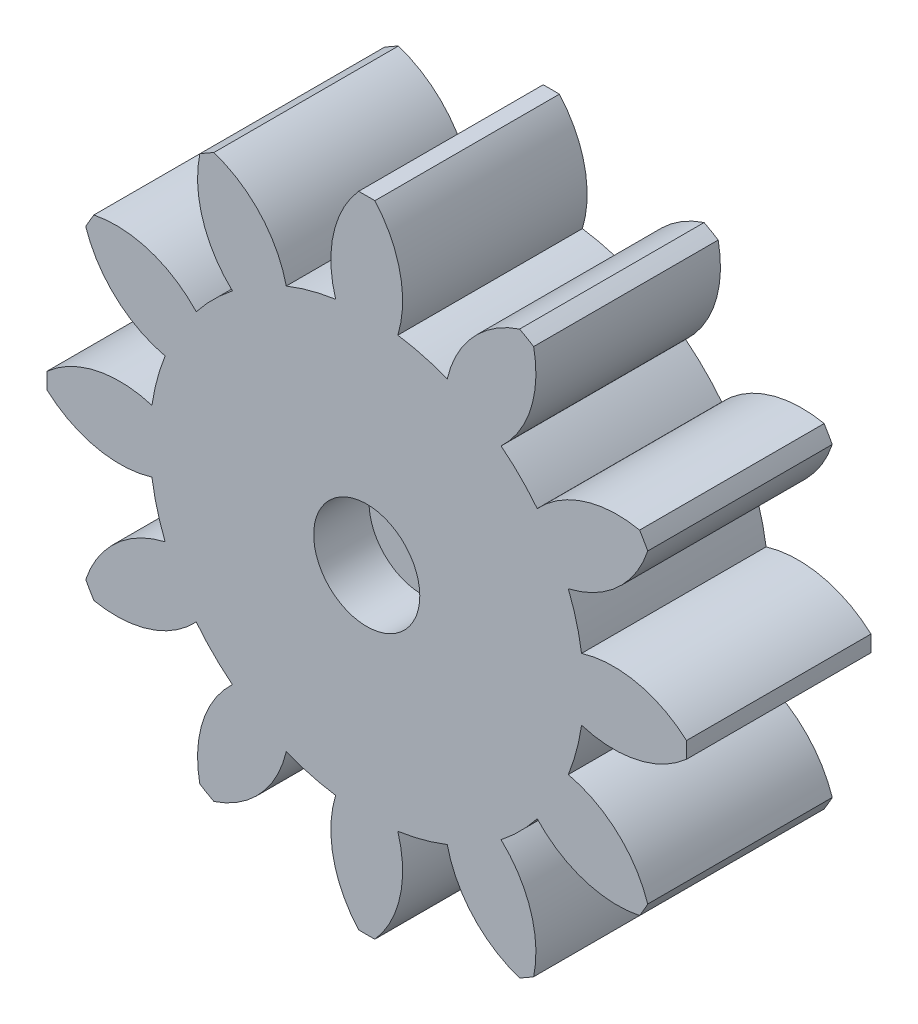
SolidWorks part; units mm, degrees
ref_plane "Front Plane" through (0, 0, 0) normal (0, 0, 1) x (1, 0, 0)
ref_plane "Top Plane" through (0, 0, 0) normal (0, 1, 0) x (1, 0, 0)
ref_plane "Right Plane" through (0, 0, 0) normal (1, 0, 0) x (0, 0, -1)
sketch "Sketch1" plane through (0, 0, 0) normal (0, 0, 1) x (1, 0, 0)
  arc A96 (10.9244, -4.3614) -> (11.6416, -1.6851) centre (0, 0) ccw
  arc A97 (11.6416, -1.6851) -> (17.3299, -0.4402) centre (13.3779, 3.9992) ccw
  arc A98 (17.3299, -0.4402) -> (17.3299, 0.4402) centre (0, 0) ccw
  arc A99 (17.3299, 0.4402) -> (11.6416, 1.6851) centre (13.3779, -3.9992) ccw
  arc A100 (11.6416, 1.6851) -> (10.9244, 4.3614) centre (0, 0) ccw
  arc A101 (10.9244, 4.3614) -> (15.2282, 8.2838) centre (9.586, 10.1524) ccw
  arc A102 (15.2282, 8.2838) -> (14.7881, 9.0462) centre (0, 0) ccw
  arc A103 (14.7881, 9.0462) -> (9.2393, 7.2801) centre (13.5852, 3.2255) ccw
  arc A104 (9.2393, 7.2801) -> (7.2801, 9.2393) centre (0, 0) ccw
  arc A105 (7.2801, 9.2393) -> (9.0462, 14.7881) centre (3.2255, 13.5852) ccw
  arc A106 (9.0462, 14.7881) -> (8.2838, 15.2282) centre (0, 0) ccw
  arc A107 (8.2838, 15.2282) -> (4.3614, 10.9244) centre (10.1524, 9.586) ccw
  arc A108 (4.3614, 10.9244) -> (1.6851, 11.6416) centre (0, 0) ccw
  arc A109 (1.6851, 11.6416) -> (0.4402, 17.3299) centre (-3.9992, 13.3779) ccw
  arc A110 (0.4402, 17.3299) -> (-0.4402, 17.3299) centre (0, 0) ccw
  arc A111 (-0.4402, 17.3299) -> (-1.6851, 11.6416) centre (3.9992, 13.3779) ccw
  arc A112 (-1.6851, 11.6416) -> (-4.3614, 10.9244) centre (0, 0) ccw
  arc A113 (-4.3614, 10.9244) -> (-8.2838, 15.2282) centre (-10.1524, 9.586) ccw
  arc A114 (-8.2838, 15.2282) -> (-9.0462, 14.7881) centre (0, 0) ccw
  arc A115 (-9.0462, 14.7881) -> (-7.2801, 9.2393) centre (-3.2255, 13.5852) ccw
  arc A116 (-7.2801, 9.2393) -> (-9.2393, 7.2801) centre (0, 0) ccw
  arc A117 (-9.2393, 7.2801) -> (-14.7881, 9.0462) centre (-13.5852, 3.2255) ccw
  arc A118 (-14.7881, 9.0462) -> (-15.2282, 8.2838) centre (0, 0) ccw
  arc A119 (-15.2282, 8.2838) -> (-10.9244, 4.3614) centre (-9.586, 10.1524) ccw
  arc A120 (-10.9244, 4.3614) -> (-11.6416, 1.6851) centre (0, 0) ccw
  arc A121 (-11.6416, 1.6851) -> (-17.3299, 0.4402) centre (-13.3779, -3.9992) ccw
  arc A122 (-17.3299, 0.4402) -> (-17.3299, -0.4402) centre (0, 0) ccw
  arc A123 (-17.3299, -0.4402) -> (-11.6416, -1.6851) centre (-13.3779, 3.9992) ccw
  arc A124 (-11.6416, -1.6851) -> (-10.9244, -4.3614) centre (0, 0) ccw
  arc A125 (-10.9244, -4.3614) -> (-15.2282, -8.2838) centre (-9.586, -10.1524) ccw
  arc A126 (-15.2282, -8.2838) -> (-14.7881, -9.0462) centre (0, 0) ccw
  arc A127 (-14.7881, -9.0462) -> (-9.2393, -7.2801) centre (-13.5852, -3.2255) ccw
  arc A128 (-9.2393, -7.2801) -> (-7.2801, -9.2393) centre (0, 0) ccw
  arc A129 (-7.2801, -9.2393) -> (-9.0462, -14.7881) centre (-3.2255, -13.5852) ccw
  arc A130 (-9.0462, -14.7881) -> (-8.2838, -15.2282) centre (0, 0) ccw
  arc A131 (-8.2838, -15.2282) -> (-4.3614, -10.9244) centre (-10.1524, -9.586) ccw
  arc A132 (-4.3614, -10.9244) -> (-1.6851, -11.6416) centre (0, 0) ccw
  arc A133 (-1.6851, -11.6416) -> (-0.4402, -17.3299) centre (3.9992, -13.3779) ccw
  arc A134 (-0.4402, -17.3299) -> (0.4402, -17.3299) centre (0, 0) ccw
  arc A135 (0.4402, -17.3299) -> (1.6851, -11.6416) centre (-3.9992, -13.3779) ccw
  arc A136 (1.6851, -11.6416) -> (4.3614, -10.9244) centre (0, 0) ccw
  arc A137 (4.3614, -10.9244) -> (8.2838, -15.2282) centre (10.1524, -9.586) ccw
  arc A138 (8.2838, -15.2282) -> (9.0462, -14.7881) centre (0, 0) ccw
  arc A139 (9.0462, -14.7881) -> (7.2801, -9.2393) centre (3.2255, -13.5852) ccw
  arc A140 (7.2801, -9.2393) -> (9.2393, -7.2801) centre (0, 0) ccw
  arc A141 (9.2393, -7.2801) -> (14.7881, -9.0462) centre (13.5852, -3.2255) ccw
  arc A142 (14.7881, -9.0462) -> (15.2282, -8.2838) centre (0, 0) ccw
  arc A143 (15.2282, -8.2838) -> (10.9244, -4.3614) centre (9.586, -10.1524) ccw
extrude "Boss-Extrude1" add sketch "Sketch1" along normal blind 10
sketch "Sketch3" plane through (0, 0, 10) normal (0, 0, 1) x (1, 0, 0)
  circle A0 centre (0, 0) radius 2.875
  dimension "D1" = 5.75
extrude "Cut-Extrude1" cut sketch "Sketch3" against normal blind 3
sketch "Sketch4" plane through (0, 0, 0) normal (0, 0, -1) x (-1, 0, 0)
  circle A0 centre (0, 0) radius 2.875 construction
  circle A1 centre (0, 0) radius 2.875
extrude "Cut-Extrude2" cut sketch "Sketch4" against normal offset from surface (5 mm away) 2 up to face at (2.875, 0, 7)
sketch "Sketch5" plane through (0, 0, 5) normal (0, 0, -1) x (-1, 0, 0)
  circle A0 centre (0, 0) radius 1.375
  dimension "D1" = 2.75
extrude "Cut-Extrude3" cut sketch "Sketch5" against normal up to next
sketch "Sketch6" plane through (0, 0, 0) normal (0, 0, -1) x (-1, 0, 0)
  text T0 "<i>.75</i>" font "Century Gothic" height in points 22
extrude "Cut-Extrude4" cut sketch "Sketch6" against normal blind 0.4
sketch "Sketch7" plane through (0, 0, 10) normal (0, 0, 1) x (1, 0, 0)
  point P0 (0, 0)
sketch "Sketch8" plane through (0, 0, 10) normal (0, 0, 1) x (1, 0, 0)
  line L0 (0, 0) -> (0, -17.3355) construction
  arc A0 (-0.4402, -17.3299) -> (0.4402, -17.3299) centre (0, 0) ccw construction
